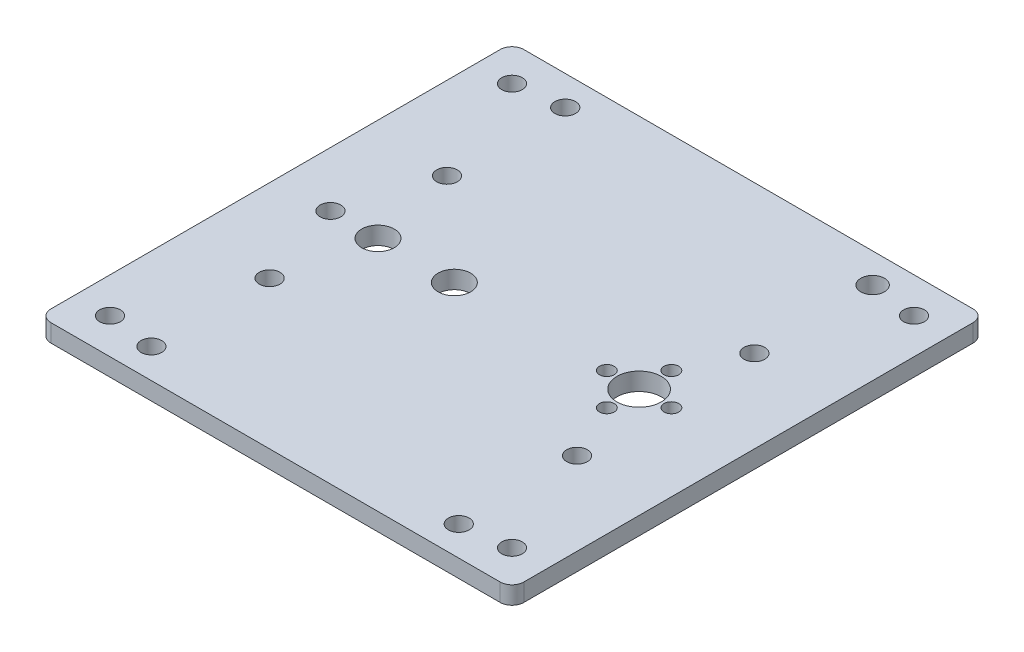
SolidWorks part; units mm, degrees
ref_plane "Front Plane" through (0, 0, 0) normal (0, 0, 1) x (1, 0, 0)
ref_plane "Top Plane" through (0, 0, 0) normal (0, 1, 0) x (1, 0, 0)
ref_plane "Right Plane" through (0, 0, 0) normal (1, 0, 0) x (0, 0, -1)
sketch "Sketch1" plane through (0, 0, 0) normal (0, 1, 0) x (1, 0, 0)
  line L1 (0, 0) -> (80, 0)
  line L2 (0, 0) -> (0, 80)
  line L3 (0, 80) -> (80, 80)
  line L4 (80, 0) -> (80, 80)
  dimension "D1" = 80
  dimension "D2" = 80
extrude "Boss-Extrude1" add sketch "Sketch1" along normal blind 3
sketch "Sketch2" plane through (0, 3, 0) normal (0, 1, 0) x (1, 0, 0)
  line L0 (0, 40) -> (80, 40) construction
  line L1 (0, 80) -> (0, 0) construction
  line L2 (80, 0) -> (80, 80) construction
  circle A0 centre (9.29, 40) radius 1.75
  circle A1 centre (17.33, 40) radius 2.75
  dimension "D2" = 3.5
  dimension "D4" = 5.5
  dimension "D1" = 9.29
  dimension "D3" = 8.04
extrude "Cut-Extrude1" cut sketch "Sketch2" against normal through all
sketch "Sketch3" plane through (0, 3, 0) normal (0, 1, 0) x (1, 0, 0)
  line L0 (0, 40) -> (80, 40) construction
  line L1 (0, 80) -> (0, 0) construction
  line L2 (80, 0) -> (80, 80) construction
  circle A0 centre (61.5, 40) radius 3.75
  dimension "D2" = 7.5
  dimension "D1" = 18.5
extrude "Cut-Extrude2" cut sketch "Sketch3" against normal through all
sketch "Sketch4" plane through (0, 3, 0) normal (0, 1, 0) x (1, 0, 0)
  line L0 (0, 40) -> (80, 40) construction
  line L1 (0, 80) -> (0, 0) construction
  line L2 (80, 0) -> (80, 80) construction
  line L3 (61.5, 40) -> (61.5, 0) construction
  line L4 (61.5, 40) -> (61.5, 80) construction
  line L5 (80, 80) -> (0, 80) construction
  circle A0 centre (66.96, 40) radius 1.25
  circle A1 centre (56.04, 40) radius 1.25
  circle A2 centre (61.5, 34.54) radius 1.25
  circle A3 centre (61.5, 45.46) radius 1.25
  dimension "D1" = 2.5
  dimension "D3" = 2.5
  dimension "D4" = 2.5
  dimension "D5" = 2.5
  dimension "D2" = 5.46
  dimension "D6" = 5.46
  dimension "D7" = 5.46
  dimension "D8" = 5.46
extrude "Cut-Extrude3" cut sketch "Sketch4" against normal through all
sketch "Sketch5" plane through (0, 3, 0) normal (0, 1, 0) x (1, 0, 0)
  line L0 (0, 40) -> (80, 40) construction
  line L1 (0, 80) -> (0, 0) construction
  line L2 (80, 0) -> (80, 80) construction
  circle A0 centre (30.25, 40) radius 2.75
  dimension "D2" = 5.5
  dimension "D1" = 30.25
extrude "Cut-Extrude4" cut sketch "Sketch5" against normal through all
sketch "Sketch6" plane through (0, 3, 0) normal (0, 1, 0) x (1, 0, 0)
  line L0 (40, 80) -> (40, 0) construction
  line L1 (80, 80) -> (0, 80) construction
  line L2 (0, 0) -> (80, 0) construction
  line L3 (0, 40) -> (80, 40) construction
  line L4 (0, 80) -> (0, 0) construction
  line L5 (80, 0) -> (80, 80) construction
  circle A0 centre (6, 74) radius 1.75
  circle A1 centre (74, 74) radius 1.75
  circle A2 centre (74, 6) radius 1.75
  circle A3 centre (6, 6) radius 1.75
  dimension "D3" = 3.5
  dimension "D1" = 6
  dimension "D2" = 6
extrude "Cut-Extrude5" cut sketch "Sketch6" against normal through all
fillet "Fillet1" radius 2 4 edges at (0, 1.5, -80) (80, 1.5, -80) (0, 1.5, 0) (80, 1.5, 0)
sketch "Sketch7" plane through (0, 3, 0) normal (0, 1, 0) x (1, 0, 0)
  line L0 (2, 0) -> (78, 0) construction
  line L1 (80, 2) -> (80, 78) construction
  line L2 (78, 80) -> (2, 80) construction
  line L6 (0, 78) -> (0, 2) construction
  circle A0 centre (14, 5) radius 1.75
  circle A1 centre (66, 5) radius 1.75
  circle A2 centre (66, 25) radius 1.75
  circle A3 centre (14, 25) radius 1.75
  circle A4 centre (14, 75) radius 1.75
  circle A5 centre (14, 55) radius 1.75
  circle A6 centre (66, 75) radius 2
  circle A7 centre (66, 55) radius 1.75
  dimension "D7" = 3.5
  dimension "D1" = 3.5
  dimension "D9" = 3.5
  dimension "D10" = 3.5
  dimension "D13" = 3.5
  dimension "D17" = 4
  dimension "D23" = 3.5
  dimension "D24" = 3.5
  dimension "D2" = 5
  dimension "D3" = 14
  dimension "D4" = 14
  dimension "D5" = 14
  dimension "D6" = 5
  dimension "D8" = 14
  dimension "D11" = 25
  dimension "D12" = 25
  dimension "D14" = 14
  dimension "D15" = 5
  dimension "D16" = 5
  dimension "D18" = 14
  dimension "D19" = 14
  dimension "D20" = 14
  dimension "D21" = 25
  dimension "D22" = 25
extrude "Cut-Extrude6" cut sketch "Sketch7" against normal through all
